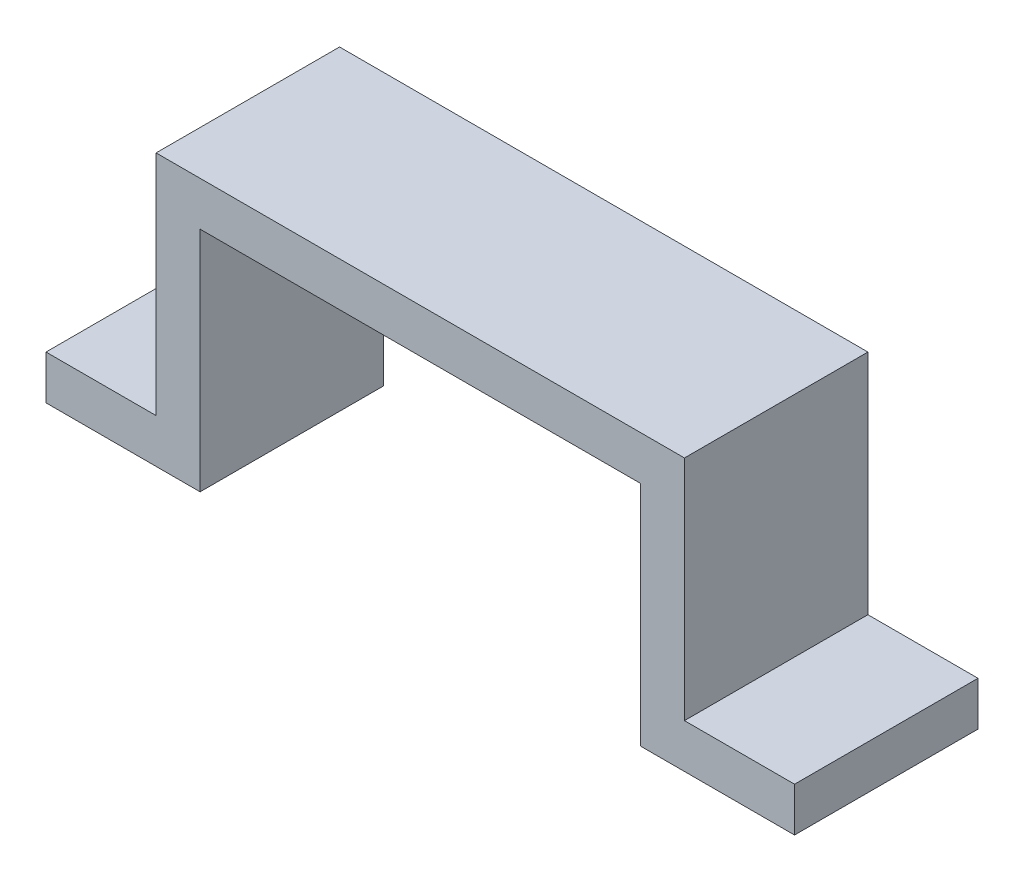
SolidWorks part; units mm, degrees
ref_plane "Front Plane" through (0, 0, 0) normal (0, 0, 1) x (1, 0, 0)
ref_plane "Top Plane" through (0, 0, 0) normal (0, 1, 0) x (1, 0, 0)
ref_plane "Right Plane" through (0, 0, 0) normal (1, 0, 0) x (0, 0, -1)
sketch "Sketch1" plane through (0, 0, 0) normal (0, 0, 1) x (1, 0, 0)
  line L0 (0, 0) -> (15, 0)
  line L1 (15, 0) -> (15, 31)
  line L2 (15, 31) -> (87, 31)
  line L3 (87, 31) -> (87, 0)
  line L4 (87, 0) -> (102, 0)
  line L5 (102, 0) -> (102, -6)
  line L6 (102, -6) -> (81, -6)
  line L7 (81, -6) -> (81, 25)
  line L8 (81, 25) -> (21, 25)
  line L9 (21, 25) -> (21, -6)
  line L10 (21, -6) -> (0, -6)
  line L11 (0, -6) -> (0, 0)
  dimension "D1" = 6
  dimension "D2" = 6
  dimension "D3" = 60
  dimension "D4" = 6
  dimension "D5" = 6
  dimension "D6" = 6
  dimension "D7" = 37
  dimension "D8" = 15
extrude "Boss-Extrude1" add sketch "Sketch1" along normal blind 25
